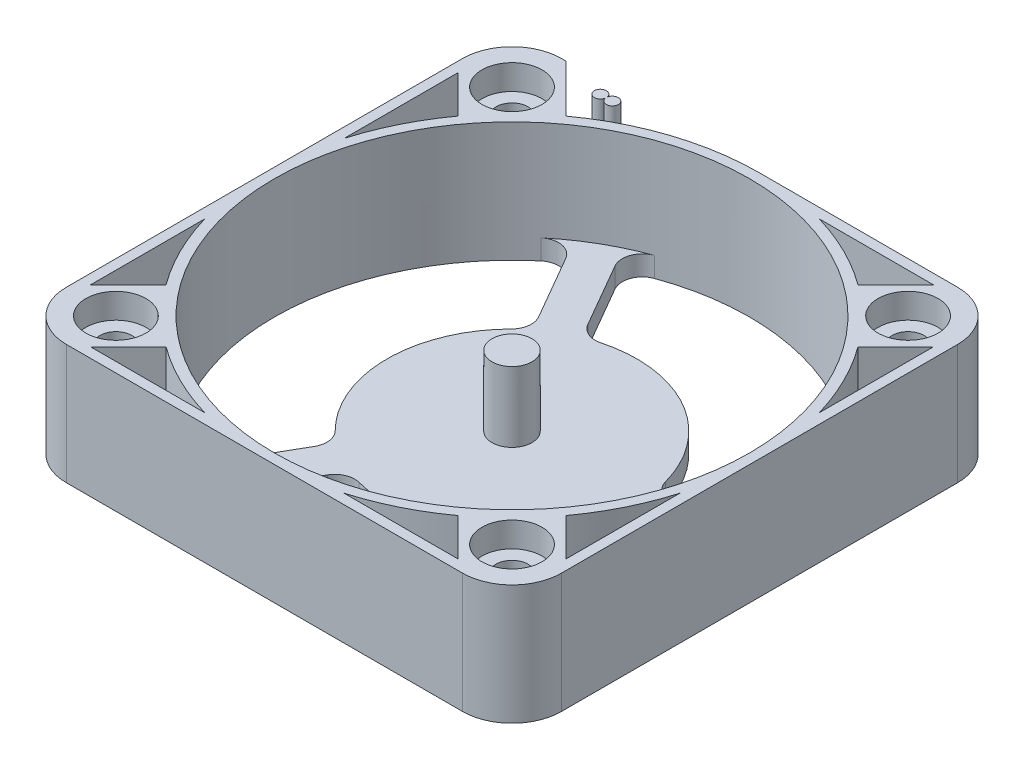
SolidWorks part; units mm, degrees
ref_plane "前视基准面" through (0, 0, 0) normal (0, 0, 1) x (1, 0, 0)
ref_plane "上视基准面" through (0, 0, 0) normal (0, 1, 0) x (1, 0, 0)
ref_plane "右视基准面" through (0, 0, 0) normal (1, 0, 0) x (0, 0, -1)
sketch "草图1" plane through (0, 0, 0) normal (0, 1, 0) x (1, 0, 0)
  line L1 (-24.75, -24.75) -> (24.75, -24.75)
  line L2 (-24.75, -24.75) -> (-24.75, 24.75)
  line L3 (-24.75, 24.75) -> (24.75, 24.75)
  line L4 (24.75, -24.75) -> (24.75, 24.75)
  line L5 (-24.75, -24.75) -> (24.75, 24.75) construction
  line L6 (-24.75, 24.75) -> (24.75, -24.75) construction
  circle A0 centre (0, 0) radius 23.75
  point P0 (0, 0)
  dimension "D2" = 47.5
  dimension "D1" = 49.5
extrude "凸台-拉伸1" add sketch "草图1" along normal blind 11.98
sketch "草图2" plane through (0, 11.98, 0) normal (0, 1, 0) x (1, 0, 0)
  line L0 (0, 0) -> (-26.3476, 26.3476) construction
  circle A0 centre (-19.799, 19.799) radius 3
  dimension "D1" = 6
  dimension "D2" = 28
extrude "切除-拉伸1" cut sketch "草图2" against normal blind 2.5
sketch "草图3" plane through (0, 9.48, 0) normal (0, 1, 0) x (1, 0, 0)
  circle A0 centre (-19.799, 19.799) radius 1.6
  dimension "D1" = 3.2
extrude "切除-拉伸2" cut sketch "草图3" against normal through all
sketch "草图4" plane through (0, 11.98, 0) normal (0, 1, 0) x (1, 0, 0)
  line L0 (-24.75, 19.799) -> (-24.75, 24.75)
  line L1 (24.75, 24.75) -> (-24.75, 24.75) construction
  line L2 (-24.75, 24.75) -> (-19.799, 24.75)
  arc A0 (-19.799, 24.75) -> (-24.75, 19.799) centre (-19.799, 19.799) ccw
extrude "切除-拉伸3" cut sketch "草图4" against normal through all
sketch "草图5" plane through (0, 11.98, 0) normal (0, 1, 0) x (1, 0, 0)
  line L0 (-23.75, 18.376) -> (-19.9804, 14.6064)
  line L1 (-18.376, 23.75) -> (-6.9642, 23.75)
  line L2 (-18.376, 23.75) -> (-14.6064, 19.9804)
  line L3 (-23.75, 19.799) -> (-23.75, -24.75)
  line L4 (-23.75, 18.376) -> (-23.75, 6.9642)
  line L5 (0, 0) -> (-32.8249, 32.8249) construction
  arc A0 (-14.6064, 19.9804) -> (-6.9642, 23.75) centre (0, 0) cw
  circle A4 centre (0, 0) radius 24.75
  arc A5 (-19.9804, 14.6064) -> (-23.75, 6.9642) centre (0, 0) ccw
  dimension "D3" = 3.8
  dimension "D1" = 1
  dimension "D2" = 1
extrude "切除-拉伸4" cut sketch "草图5" against normal blind 9.5
pattern_circular "阵列(圆周)1" count 4 over 360 about axis through (0, 0, 0) along (0, 1, 0) of "切除-拉伸1", "切除-拉伸2", "切除-拉伸3", "切除-拉伸4"
sketch "草图7" plane through (0, 0, 0) normal (0, -1, 0) x (1, 0, 0)
  circle A0 centre (0, 0) radius 12.5
  dimension "D1" = 25
extrude "凸台-拉伸2" add sketch "草图7" against normal blind 2 separate body
sketch "草图8" plane through (0, 0, 0) normal (0, -1, 0) x (1, 0, 0)
  line L0 (0, 0) -> (36.5984, 0) construction
  line L1 (23.6817, -1.8) -> (12.3697, -1.8)
  line L2 (23.6817, 1.8) -> (12.3697, 1.8)
  circle A2 centre (0, 0) radius 23.75
  arc A3 (23.6817, -1.8) -> (23.6817, 1.8) centre (0, 0) ccw
  circle A5 centre (0, 0) radius 12.5
  arc A6 (12.3697, -1.8) -> (12.3697, 1.8) centre (0, 0) ccw
  dimension "D1" = 3.6
  dimension "D2" = 0
  dimension "D3" = 0
extrude "凸台-拉伸3" add sketch "草图8" against normal up to surface (2 mm away) up to face at (0, 2, -12.5)
fillet "圆角2" radius 2 4 edges at (12.3697, 1, 1.8) (23.6817, 1, 1.8) (12.3697, 1, -1.8) (23.6817, 1, -1.8)
pattern_circular "阵列(圆周)2" count 3 over 360 about axis through (0, 0, 0) along (0, 1, 0) of "凸台-拉伸3", "圆角2"
sketch "草图9" plane through (0, 2, 0) normal (0, 1, 0) x (1, 0, 0)
  circle A0 centre (0, 0) radius 2
  dimension "D1" = 4
extrude "凸台-拉伸4" add sketch "草图9" along normal blind 7
sketch "草图10" plane through (0, 11.98, 0) normal (0, 1, 0) x (1, 0, 0)
  line L1 (-14.6064, 19.9804) -> (-19.376, 24.75)
  line L4 (19.799, 24.75) -> (-19.799, 24.75)
  line L5 (0, 24.75) -> (-19.376, 24.75)
  arc A0 (0, 24.75) -> (-14.6064, 19.9804) centre (0, 0) ccw
  dimension "D1" = 0
extrude "切除-拉伸5" cut sketch "草图10" against normal up to surface (9.5 mm away) up to face at (-13.37, 2.48, -22.6039)
sketch "草图11" plane through (0, 2.48, 0) normal (0, 1, 0) x (1, 0, 0)
  line L1 (-13.6629, 23.2408) -> (-13.6918, 23.2408)
  line L3 (-13.6629, 22.9792) -> (-13.6918, 22.9792)
  arc A0 (-13.6918, 23.2408) -> (-13.6918, 22.9792) centre (-14.2774, 23.11) ccw
  arc A1 (-13.6629, 22.9792) -> (-13.6629, 23.2408) centre (-13.0774, 23.11) ccw
  point P4 (-13.6774, 23.11)
  dimension "D1" = 1.2
extrude "凸台-拉伸5" add sketch "草图11" along normal blind 10
